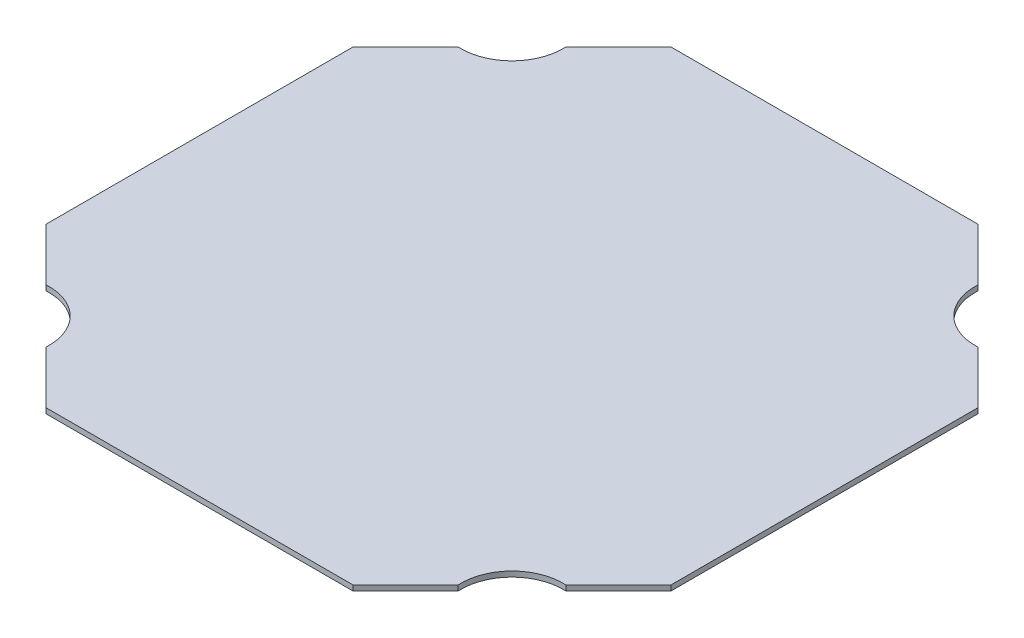
SolidWorks part; units mm, degrees
material "Acrylic (Medium-high impact)"
ref_plane "Front Plane" through (0, 0, 0) normal (0, 0, 1) x (1, 0, 0)
ref_plane "Top Plane" through (0, 0, 0) normal (0, 1, 0) x (1, 0, 0)
ref_plane "Right Plane" through (0, 0, 0) normal (1, 0, 0) x (0, 0, -1)
sketch "Sketch1" plane through (0, 0, 0) normal (0, 1, 0) x (1, 0, 0)
  line L2 (0, 0) -> (749.3, 0)
  line L3 (0, 0) -> (0, 749.3)
  line L5 (749.3, 0) -> (749.3, 749.3)
  line L9 (558.8, 749.3) -> (621.7211, 686.3789)
  line L14 (686.3789, 621.7211) -> (749.3, 558.8)
  line L16 (374.65, 749.3) -> (374.65, 0) construction
  line L17 (749.3, 749.3) -> (0, 749.3)
  line L67 (62.9211, 621.7211) -> (0, 558.8)
  line L68 (749.3, 374.65) -> (0, 374.65) construction
  line L73 (190.5, 749.3) -> (127.5789, 686.3789)
  line L74 (686.3789, 127.5789) -> (749.3, 190.5)
  line L75 (558.8, 0) -> (621.7211, 62.9211)
  line L77 (62.9211, 127.5789) -> (0, 190.5)
  line L78 (190.5, 0) -> (127.5789, 62.9211)
  arc A1 (621.7211, 686.3789) -> (686.3789, 621.7211) centre (682.7512, 682.7512) ccw
  arc A2 (127.5789, 686.3789) -> (62.9211, 621.7211) centre (66.5488, 682.7512) cw
  arc A3 (621.7211, 62.9211) -> (686.3789, 127.5789) centre (682.7512, 66.5488) cw
  arc A4 (127.5789, 62.9211) -> (62.9211, 127.5789) centre (66.5488, 66.5488) ccw
  dimension "D1" = 749.3
  dimension "D3" = 61.1379
  dimension "D2" = 749.3
  dimension "D4" = 91.44
  dimension "D5" = 190.5
  dimension "D6" = 190.5
extrude "Boss-Extrude1" add sketch "Sketch1" along normal blind 6.35 contours A4 L78 L2 L75 A3 L74 L5 L14 A1 L9 L17 L73 A2 L67 L3 L77
sketch "Sketch2" [suppressed] plane through (0, 6.35, 0) normal (0, 1, 0) x (1, 0, 0)
  line L0 (647.7, 0) -> (647.7, 25.4)
  line L1 (647.7, 25.4) -> (101.6, 25.4)
  line L2 (101.6, 25.4) -> (101.6, 0)
  line L3 (101.6, 0) -> (647.7, 0)
  line L4 (546.1, 723.9) -> (520.7, 723.9)
  line L5 (520.7, 723.9) -> (520.7, 25.4)
  line L17 (520.7, 25.4) -> (546.1, 25.4)
  line L18 (546.1, 25.4) -> (546.1, 723.9)
  line L19 (228.6, 723.9) -> (203.2, 723.9)
  line L20 (203.2, 723.9) -> (203.2, 25.4)
  line L21 (203.2, 25.4) -> (228.6, 25.4)
  line L22 (228.6, 25.4) -> (228.6, 723.9)
  line L23 (647.7, 723.9) -> (647.7, 749.3)
  line L24 (647.7, 749.3) -> (101.6, 749.3)
  line L25 (101.6, 749.3) -> (101.6, 723.9)
  line L26 (101.6, 723.9) -> (647.7, 723.9)
  line L27 (558.8, 749.3) -> (190.5, 749.3) construction
  line L28 (0, 190.5) -> (0, 558.8) construction
  dimension "D1" = 25.4
  dimension "D2" = 25.4
  dimension "D3" = 749.3
  dimension "D4" = 546.1
  dimension "D5" = 101.6
  dimension "D6" = 101.6
  dimension "D7" = 101.6
  dimension "D8" = 203.2
sketch "Sketch3" [suppressed] plane through (0, 6.35, 0) normal (0, 1, 0) x (1, 0, 0)
  line L0 (171.45, 749.3) -> (260.35, 749.3)
  line L1 (647.7, 749.3) -> (101.6, 749.3) construction
  line L2 (558.8, 749.3) -> (190.5, 749.3) construction
  line L3 (260.35, 749.3) -> (260.35, 723.9)
  line L4 (101.6, 723.9) -> (647.7, 723.9) construction
  line L5 (260.35, 723.9) -> (228.6, 723.9)
  line L6 (228.6, 723.9) -> (228.6, 685.8)
  line L7 (228.6, 25.4) -> (228.6, 723.9) construction
  line L8 (228.6, 685.8) -> (203.2, 685.8)
  line L9 (203.2, 723.9) -> (203.2, 25.4) construction
  line L10 (203.2, 685.8) -> (203.2, 723.9)
  line L11 (203.2, 723.9) -> (171.45, 723.9)
  line L12 (171.45, 723.9) -> (171.45, 749.3)
  line L13 (546.1, 723.9) -> (546.1, 685.8)
  line L14 (546.1, 25.4) -> (546.1, 723.9) construction
  line L15 (546.1, 685.8) -> (520.7, 685.8)
  line L16 (520.7, 723.9) -> (520.7, 25.4) construction
  line L17 (520.7, 685.8) -> (520.7, 723.9)
  line L18 (520.7, 723.9) -> (488.95, 723.9)
  line L19 (488.95, 723.9) -> (488.95, 749.3)
  line L20 (488.95, 749.3) -> (577.85, 749.3)
  line L21 (577.85, 749.3) -> (577.85, 723.9)
  line L22 (577.85, 723.9) -> (546.1, 723.9)
  line L23 (203.2, 25.4) -> (203.2, 63.5)
  line L24 (203.2, 63.5) -> (228.6, 63.5)
  line L25 (228.6, 63.5) -> (228.6, 25.4)
  line L26 (228.6, 25.4) -> (260.35, 25.4)
  line L27 (647.7, 25.4) -> (101.6, 25.4) construction
  line L28 (260.35, 25.4) -> (260.35, 0)
  line L29 (190.5, 0) -> (558.8, 0) construction
  line L30 (260.35, 0) -> (171.45, 0)
  line L31 (101.6, 0) -> (647.7, 0) construction
  line L32 (171.45, 0) -> (171.45, 25.4)
  line L33 (171.45, 25.4) -> (203.2, 25.4)
  line L34 (520.7, 63.5) -> (546.1, 63.5)
  line L35 (546.1, 63.5) -> (546.1, 25.4)
  line L36 (546.1, 25.4) -> (577.85, 25.4)
  line L37 (577.85, 25.4) -> (577.85, 0)
  line L38 (577.85, 0) -> (488.95, 0)
  line L39 (488.95, 0) -> (488.95, 25.4)
  line L40 (488.95, 25.4) -> (520.7, 25.4)
  line L41 (520.7, 25.4) -> (520.7, 63.5)
  dimension "D1" = 88.9
  dimension "D2" = 38.1
extrude "Cut-Extrude1" [suppressed] cut sketch "Sketch3" against normal through all both and the other way through all
